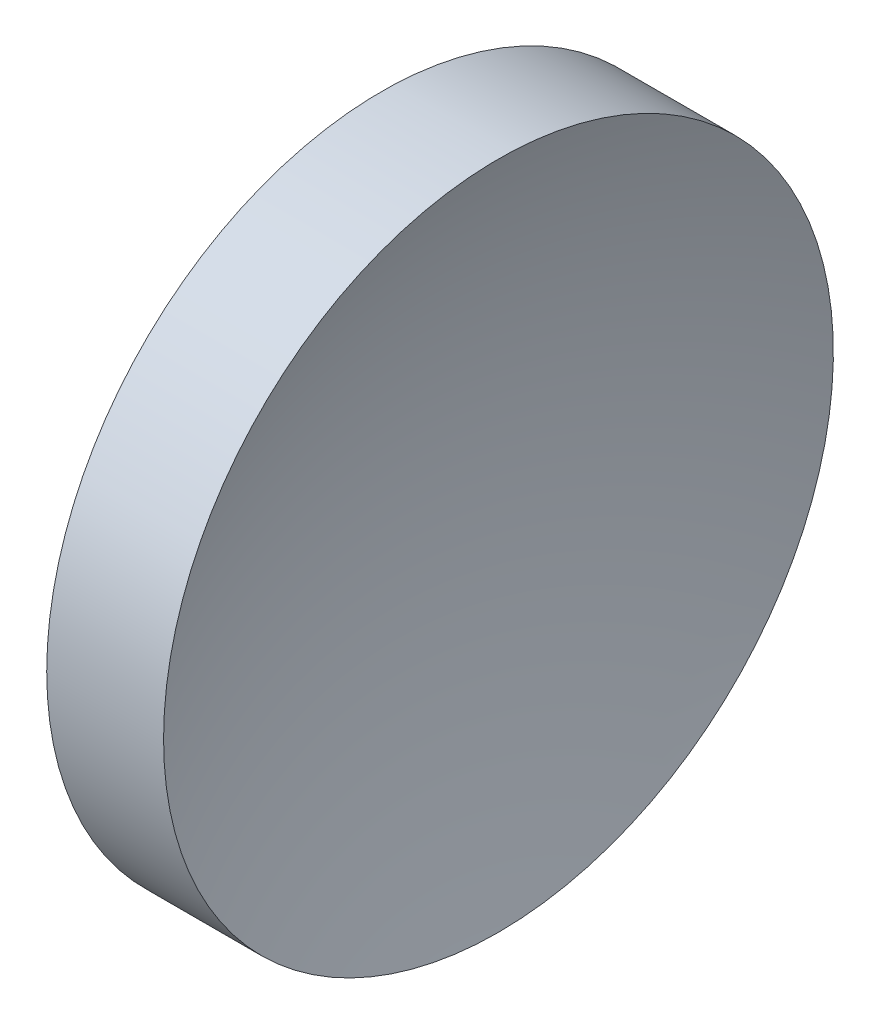
SolidWorks part; units mm, degrees
ref_plane "前视基准面" through (0, 0, 0) normal (0, 0, 1) x (1, 0, 0)
ref_plane "上视基准面" through (0, 0, 0) normal (0, 1, 0) x (1, 0, 0)
ref_plane "右视基准面" through (0, 0, 0) normal (1, 0, 0) x (0, 0, -1)
sketch "草图1" plane through (0, 0, 0) normal (0, 0, 1) x (1, 0, 0)
  line L0 (111.9552, 71.194) -> (132.4701, 71.194) construction
  line L1 (119.3629, 71.194) -> (119.3629, 83.894)
  line L2 (119.3629, 83.894) -> (123.7939, 83.894)
  line L3 (121.3629, 71.194) -> (119.3629, 71.194)
  arc A0 (123.7939, 83.894) -> (121.3629, 71.194) centre (155.7529, 71.194) ccw
revolve "旋转1" add sketch "草图1" angle 360 about L0
